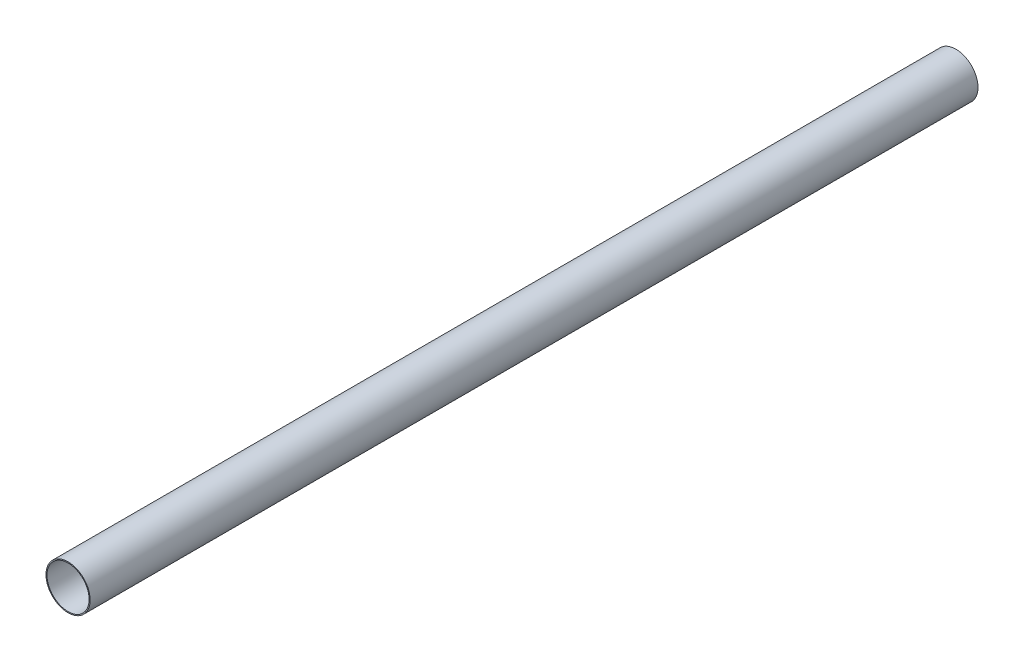
SolidWorks part; units mm, degrees
ref_plane "Front" through (0, 0, 0) normal (0, 0, 1) x (1, 0, 0)
ref_plane "Top" through (0, 0, 0) normal (0, 1, 0) x (1, 0, 0)
ref_plane "Side" through (0, 0, 0) normal (1, 0, 0) x (0, 0, -1)
sketch "PipeSketch" plane through (0, 0, 0) normal (0, 0, 1) x (1, 0, 0)
  circle A0 centre (0, 0) radius 136.525
  circle A1 centre (0, 0) radius 130.175
  dimension "OuterDiameter" = 273.05
  dimension "InnerDiameter" = 260.35
extrude "Extrusion" add sketch "PipeSketch" along normal blind 5486.4
sketch "FilterSketch" plane through (0, 0, 0) normal (0, 0, 1) x (1, 0, 0)
  circle A0 centre (0, 0) radius 127 construction
  dimension "NominalDiameter" = 254
